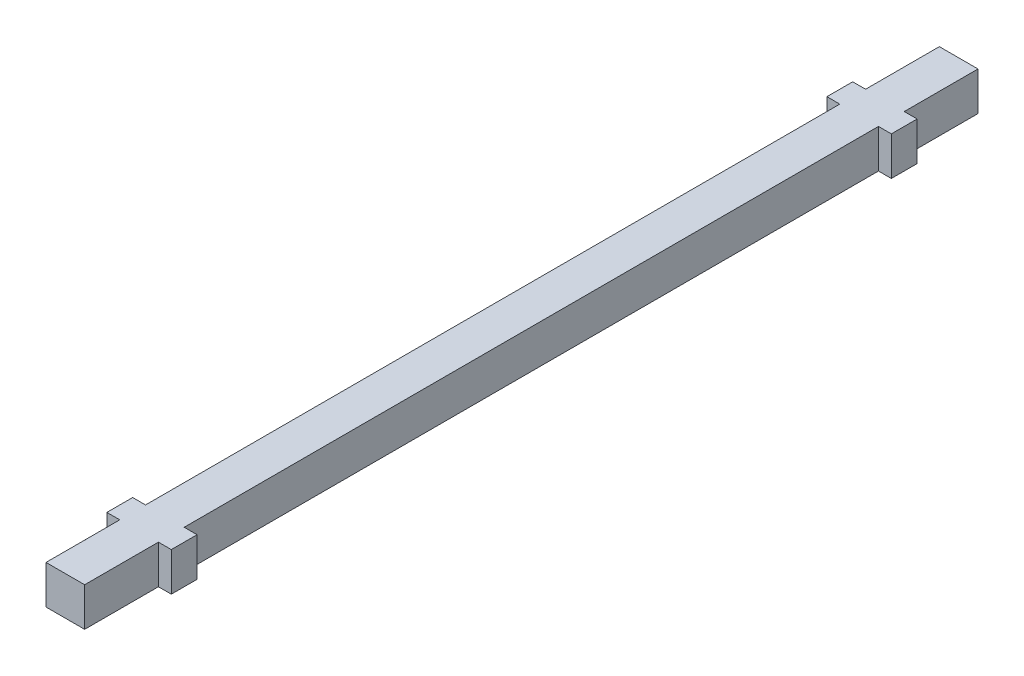
SolidWorks part; units mm, degrees
ref_plane "Front Plane" through (0, 0, 0) normal (0, 0, 1) x (1, 0, 0)
ref_plane "Top Plane" through (0, 0, 0) normal (0, 1, 0) x (1, 0, 0)
ref_plane "Right Plane" through (0, 0, 0) normal (1, 0, 0) x (0, 0, -1)
sketch "Sketch1" plane through (0, 0, 0) normal (0, 0, 1) x (1, 0, 0)
  line L1 (-4.5, -4.5) -> (4.5, -4.5)
  line L2 (-4.5, -4.5) -> (-4.5, 4.5)
  line L3 (-4.5, 4.5) -> (4.5, 4.5)
  line L4 (4.5, -4.5) -> (4.5, 4.5)
  line L5 (-4.5, -4.5) -> (4.5, 4.5) construction
  line L6 (-4.5, 4.5) -> (4.5, -4.5) construction
  point P0 (0, 0)
  dimension "D1" = 9
extrude "Boss-Extrude1" add sketch "Sketch1" along normal mid plane 208
sketch "Sketch2" plane through (0, 0, 0) normal (0, 1, 0) x (1, 0, 0)
  line L0 (4.5, -104) -> (4.5, 104) construction
  line L1 (4.5, 86.825) -> (7.5, 86.825)
  line L2 (4.5, 86.825) -> (4.5, -86.825)
  line L3 (4.5, -86.825) -> (7.5, -86.825)
  line L4 (7.5, 86.825) -> (7.5, -86.825)
  line L5 (-4.5, -104) -> (-4.5, 104) construction
  line L6 (-4.5, 86.825) -> (-7.5, 86.825)
  line L7 (-4.5, 86.825) -> (-4.5, -86.825)
  line L8 (-4.5, -86.825) -> (-7.5, -86.825)
  line L9 (-7.5, 86.825) -> (-7.5, -86.825)
  line L10 (7.5, 80.825) -> (4.5, 80.825)
  line L11 (-4.5, 80.825) -> (-7.5, 80.825)
  line L12 (-7.5, -80.825) -> (-4.5, -80.825)
  line L13 (4.5, -80.825) -> (7.5, -80.825)
  line L14 (4.5, 104) -> (-4.5, 104) construction
  point P12 (7.5, 0)
  dimension "D1" = 3
  dimension "D2" = 17.175
  dimension "D3" = 6
  dimension "D4" = 6
extrude "Boss-Extrude2" add sketch "Sketch2" along normal mid plane 9 contours L12 L9 L8 L7 | L13 L2 L3 L4 | L10 L4 L1 L2 | L11 L7 L6 L9
